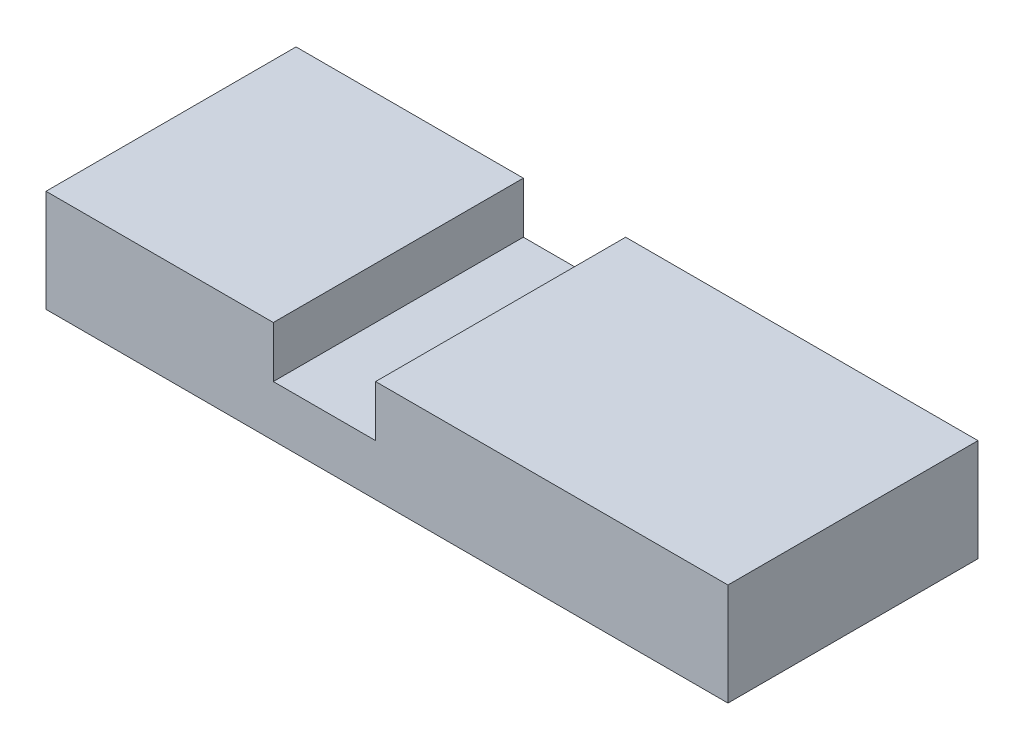
SolidWorks part; units mm, degrees
ref_plane "Front Plane" through (0, 0, 0) normal (0, 0, 1) x (1, 0, 0)
ref_plane "Top Plane" through (0, 0, 0) normal (0, 1, 0) x (1, 0, 0)
ref_plane "Right Plane" through (0, 0, 0) normal (1, 0, 0) x (0, 0, -1)
sketch "Sketch1" plane through (0, 0, 0) normal (0, 1, 0) x (1, 0, 0)
  line L0 (0, 0) -> (-120, 0)
  line L1 (-120, 0) -> (-120, 44)
  line L2 (-120, 44) -> (0, 44)
  line L3 (0, 0) -> (0, 44)
  dimension "D1" = 120
  dimension "D2" = 44
extrude "Extrude1" add sketch "Sketch1" along normal blind 18
sketch "Sketch2" plane through (0, 0, 0) normal (0, 0, 1) x (1, 0, 0)
  line L0 (-80, 18) -> (-80, 9)
  line L1 (-120, 18) -> (0, 18) construction
  line L2 (-80, 9) -> (-62, 9)
  line L3 (-62, 9) -> (-62, 18)
  line L4 (-62, 18) -> (-80, 18)
  line L5 (-120, 18) -> (-120, 0) construction
  dimension "D1" = 18
  dimension "D2" = 9
  dimension "D3" = 40
extrude "Extrude2" cut sketch "Sketch2" against normal up to next
